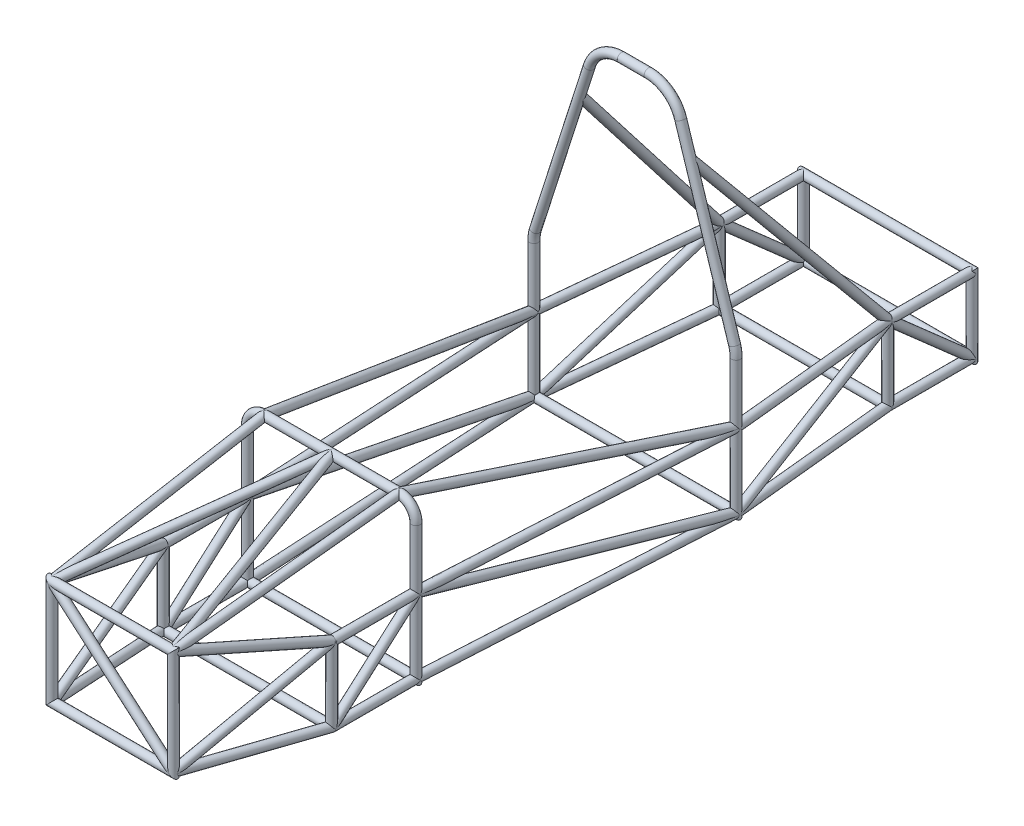
SolidWorks part; units mm, degrees
ref_plane "Front Plane" through (0, 0, 0) normal (0, 0, 1) x (1, 0, 0)
ref_plane "Top Plane" through (0, 0, 0) normal (0, 1, 0) x (1, 0, 0)
ref_plane "Right Plane" through (0, 0, 0) normal (1, 0, 0) x (0, 0, -1)
sketch "Sketch1" plane through (0, 0, 0) normal (0, 0, 1) x (1, 0, 0)
  line L0 (0, 0) -> (0, 400)
  line L1 (4.7576, 430.4776) -> (164.7576, 930.4776)
  line L2 (260, 1000) -> (340, 1000)
  line L3 (435.2424, 930.4776) -> (595.2424, 430.4776)
  line L4 (600, 400) -> (600, 0)
  line L5 (600, 0) -> (0, 0)
  line L6 (300, -975.9464) -> (300, 49024.0536) construction
  arc A0 (595.2424, 430.4776) -> (600, 400) centre (500, 400) cw
  arc A1 (0, 400) -> (4.7576, 430.4776) centre (100, 400) cw
  arc A2 (340, 1000) -> (435.2424, 930.4776) centre (340, 900) cw
  arc A3 (164.7576, 930.4776) -> (260, 1000) centre (260, 900) cw
  dimension "D2" = 100
  dimension "D3" = 100
  dimension "D1" = 600
  dimension "D4" = 300
  dimension "D5" = 400
  dimension "D6" = 80
  dimension "D7" = 1000
sketch "Sketch3" plane through (0, 0, 0) normal (0, 1, 0) x (1, 0, 0)
  line L0 (300, -1107.0637) -> (300, 51069.4933) construction
  dimension "D1" = 300
sketch3d "3DSketch26"
  line L0 (0, 0, 0) -> (50, 0, -500)
  line L2 (550, 0, -500) -> (600, 0, 0)
  line L3 (550, 0, -500) -> (50, 0, -500)
  line L4 (600, 0, 0) -> (0, 0, 0) construction
  dimension "D1" = 500
  dimension "D2" = 500
sketch3d "3DSketch30"
  line L0 (50, 0, -500) -> (50, 220, -500)
  line L2 (550, 220, -500) -> (550, 0, -500)
  dimension "D1" = 220
sketch3d "3DSketch33"
  line L0 (50, 0, -500) -> (50, 0, -750)
  line L1 (50, 0, -750) -> (550, 0, -750)
  line L2 (550, 0, -750) -> (550, 0, -500)
  line L3 (550, 0, -500) -> (50, 0, -500) construction
  dimension "D1" = 250
sketch3d "3DSketch34"
  line L0 (50, 0, -750) -> (50, 220, -750)
  line L1 (50, 220, -750) -> (550, 220, -750)
  line L2 (550, 220, -750) -> (550, 0, -750)
  dimension "D1" = 220
sketch3d "3DSketch35"
  line L0 (50, 220, -500) -> (50, 220, -750)
  line L1 (50, 220, -500) -> (50, 0, -750)
  line L2 (550, 220, -500) -> (550, 220, -750)
  line L3 (550, 220, -500) -> (550, 0, -750)
sketch3d "3DSketch36"
  line L0 (600, 0, 0) -> (550, 220, -500)
  line L1 (0, 0, 0) -> (50, 220, -500)
ref_plane "Plane1" through (0, 0, 900) normal (0, 0, 1) x (1, 0, 0)
sketch "Sketch5" plane through (0, 0, 900) normal (0, 0, 1) x (1, 0, 0)
  line L0 (50, 0) -> (550, 0)
  line L1 (600, 0) -> (0, 0) construction
  line L2 (550, 0) -> (550, 400)
  line L3 (500, 450) -> (100, 450)
  line L4 (50, 400) -> (50, 0)
  arc A0 (550, 400) -> (500, 450) centre (500, 400) ccw
  arc A1 (100, 450) -> (50, 400) centre (100, 400) ccw
  dimension "D1" = 50
  dimension "D2" = 450
  dimension "D3" = 500
  dimension "D4" = 50
sketch3d "3DSketch42"
  line L0 (0, 0, 0) -> (50, 0, 900)
  line L1 (600, 0, 0) -> (550, 0, 900)
sketch3d "3DSketch43"
  line L0 (600, 220, 0) -> (550, 220, 900)
  line L1 (600, 400, 0) -> (600, 0, 0) construction
  line L2 (550, 0, 900) -> (550, 400, 900) construction
  line L3 (550, 220, 900) -> (600, 0, 0)
  line L4 (0, 220, 0) -> (50, 220, 900)
  line L5 (0, 0, 0) -> (0, 400, 0) construction
  line L6 (50, 400, 900) -> (50, 0, 900) construction
  line L7 (50, 220, 900) -> (0, 0, 0)
  dimension "D1" = 220
  dimension "D2" = 220
  dimension "D3" = 220
  dimension "D4" = 220
sketch3d "3DSketch44"
  line L0 (600, 220, 0) -> (500, 450, 900)
  line L1 (0, 220, 0) -> (100, 450, 900)
sketch3d "3DSketch45"
  line L0 (600, 220, 0) -> (550, 220, -500)
  line L1 (0, 220, 0) -> (50, 220, -500)
sketch3d "3DSketch46"
  line L0 (50, 0, 900) -> (50, 0, 1150)
  line L1 (50, 0, 1150) -> (550, 0, 1150)
  line L2 (550, 0, 1150) -> (550, 0, 900)
  dimension "D1" = 250
sketch3d "3DSketch48"
  line L0 (50, 0, 1150) -> (50, 220, 1150)
  line L1 (50, 220, 1150) -> (50, 220, 900)
  line L2 (50, 400, 900) -> (50, 0, 900) construction
  line L3 (50, 0, 1150) -> (50, 220, 900)
  line L4 (550, 0, 1150) -> (550, 220, 1150)
  line L5 (550, 220, 1150) -> (550, 220, 900)
  line L6 (550, 0, 900) -> (550, 400, 900) construction
  line L7 (550, 220, 900) -> (550, 0, 1150)
  dimension "D1" = 220
ref_plane "Plane2" through (0, 0, 1550) normal (0, 0, 1) x (1, 0, 0)
sketch "Sketch6" plane through (0, 0, 1550) normal (0, 0, 1) x (1, 0, 0)
  line L0 (120, 49) -> (480, 49)
  line L1 (480, 49) -> (480, 359)
  line L2 (480, 359) -> (120, 359)
  line L3 (120, 359) -> (120, 49)
  line L4 (0, 0) -> (0, 400) construction
  line L5 (600, 0) -> (0, 0) construction
  dimension "D1" = 360
  dimension "D2" = 310
  dimension "D3" = 120
  dimension "D4" = 49
sketch3d "3DSketch49"
  line L0 (50, 0, 1150) -> (120, 49, 1550)
  line L1 (120, 49, 1550) -> (50, 220, 1150)
  line L2 (50, 220, 1150) -> (120, 359, 1550)
  line L3 (480, 359, 1550) -> (500, 450, 900)
  line L5 (120, 359, 1550) -> (100, 450, 900)
  line L6 (480, 359, 1550) -> (550, 220, 1150)
  line L7 (550, 220, 1150) -> (480, 49, 1550)
  line L8 (480, 49, 1550) -> (480, 359, 1550) construction
  line L9 (120, 49, 1550) -> (480, 49, 1550) construction
  line L10 (480, 49, 1550) -> (550, 0, 1150)
  line L11 (480, 359, 1550) -> (300, 450, 900)
  line L12 (120, 359, 1550) -> (480, 49, 1550)
  line L14 (500, 450, 900) -> (100, 450, 900) construction
  line L15 (300, 450, 900) -> (120, 359, 1550)
sketch "Sketch7" plane through (0, 0, 0) normal (1, 0, 0) x (0, 0, -1)
  line L1 (-517.6033, 105.9189) -> (-104.7916, 369.9008) construction
  line L2 (-104.7916, 369.9008) -> (-104.7916, 649.9008) construction
  line L5 (-900, 450) -> (0, 1009.3878) construction
  line L6 (0, 1000) -> (0, 930.4776) construction
  line L7 (0, -200975.9464) -> (0, 249024.0536) construction
  line L8 (0, 1009.3878) -> (500, 220) construction
  circle A0 centre (-517.6033, 105.9189) radius 100 construction
  arc A1 (-1413.2761, -81.1513) -> (-1357.5003, 468.959) centre (-517.6033, 105.9189) cw construction
  circle A2 centre (-104.7916, 369.9008) radius 100 construction
  circle A3 centre (-104.7916, 649.9008) radius 150 construction
  dimension "D1" = 200
  dimension "D2" = 915
  dimension "D4" = 490
  dimension "D3" = 250
  dimension "D5" = 280
sketch3d "3DSketch51"
  line L0 (50, 220, -500) -> (135.8048, 840, 0)
  line L1 (4.7576, 430.4776, 0) -> (164.7576, 930.4776, 0) construction
  line L2 (550, 220, -500) -> (464.1952, 840, 0)
  line L3 (435.2424, 930.4776, 0) -> (595.2424, 430.4776, 0) construction
  line L4 (260, 1000, 0) -> (340, 1000, 0) construction
  dimension "D1" = 160
sketch3d "3DSketch52"
  line L0 (0, 649.9008, 104.7916) -> (300, 649.9008, 104.7916) construction
  circle A0 centre (300, 649.9008, 104.7916) radius 150 construction
  point P4 (300, 649.9008, 254.7916)
  dimension "D1" = 300
ref_plane "Plane3" through (600, 400, 0) normal (0, -1, 0) x (1, 0, 0)
ref_plane "Plane4" through (595.2424, 430.4776, 0) normal (0.3048, -0.9524, 0) x (0.9524, 0.3048, 0)
ref_plane "Plane5" through (435.2424, 930.4776, 0) normal (0.3048, -0.9524, 0) x (0.9524, 0.3048, 0)
ref_plane "Plane6" through (600, 400, 0) normal (0, -1, 0) x (1, 0, 0)
ref_plane "Plane7" through (600, 0, 0) normal (-0.0555, 0, 0.9985) x (0.9985, 0, 0.0555)
ref_plane "Plane8" through (600, 220, 0) normal (-0.107, 0.2462, 0.9633) x (0.9942, 0.0134, 0.107)
ref_plane "Plane9" through (600, 220, 0) normal (-0.107, 0.2462, 0.9633) x (0.9942, 0.0134, 0.107)
ref_plane "Plane11" through (600, 0, 0) normal (-0.0555, 0, 0.9985) x (0.9985, 0, 0.0555)
ref_plane "Plane12" through (600, 400, 0) normal (0, -1, 0) x (1, 0, 0)
ref_plane "Plane13" through (120, 359, 1550) normal (0.7578, -0.6525, 0) x (0.4258, 0.4945, -0.7578)
ref_plane "Plane14" through (600, 400, 0) normal (0, -1, 0) x (1, 0, 0)
other "Pipe MAIN HOOP(1)"
ref_plane "Plane15" through (600, 400, 0) normal (0, -1, 0) x (1, 0, 0)
sketch "Sketch13" plane through (600, 400, 0) normal (0, -1, 0) x (1, 0, 0)
  circle A0 centre (0, 0) radius 12.7
  circle A1 centre (0, 0) radius 10.3
  point P4 (0, 0)
  dimension "D1" = 25.4
  dimension "D2" = 2.4
other "Pipe MAIN HOOP(2)"
ref_plane "Plane16" through (550, 0, 900) normal (0, 1, 0) x (-1, 0, 0)
sketch "Sketch14" plane through (550, 0, 900) normal (0, 1, 0) x (-1, 0, 0)
  circle A0 centre (0, 0) radius 12.7
  circle A1 centre (0, 0) radius 10.3
  point P4 (0, 0)
  dimension "D1" = 25.4
  dimension "D2" = 2.4
other "Pipe SECONDARY PROFILE(1)"
ref_plane "Plane17" through (480, 49, 1550) normal (0, 1, 0) x (-1, 0, 0)
sketch "Sketch16" plane through (480, 49, 1550) normal (0, 1, 0) x (-1, 0, 0)
  circle A0 centre (0, 0) radius 12.7
  circle A1 centre (0, 0) radius 11.05
  point P4 (0, 0)
  dimension "D1" = 25.4
  dimension "D2" = 1.65
other "Pipe SECONDARY PROFILE(2)"
ref_plane "Plane18" through (600, 220, 0) normal (-0.0555, 0, 0.9985) x (0.9985, 0, 0.0555)
sketch "Sketch17" plane through (600, 220, 0) normal (-0.0555, 0, 0.9985) x (0.9985, 0, 0.0555)
  circle A0 centre (0, 0) radius 12.7
  circle A1 centre (0, 0) radius 11.05
  point P4 (0, 0)
  dimension "D1" = 25.4
  dimension "D2" = 1.65
other "Pipe SECONDARY PROFILE(3)"
ref_plane "Plane19" through (550, 220, 900) normal (0.0539, -0.2371, -0.97) x (0.9032, 0.4257, -0.0539)
sketch "Sketch18" plane through (550, 220, 900) normal (0.0539, -0.2371, -0.97) x (0.9032, 0.4257, -0.0539)
  circle A0 centre (0, 0) radius 12.7
  circle A1 centre (0, 0) radius 11.05
  point P4 (0, 0)
  dimension "D1" = 25.4
  dimension "D2" = 1.65
other "Pipe SECONDARY PROFILE(4)"
ref_plane "Plane20" through (0, 0, 0) normal (0.0555, 0, 0.9985) x (0.9985, 0, -0.0555)
sketch "Sketch19" plane through (0, 0, 0) normal (0.0555, 0, 0.9985) x (0.9985, 0, -0.0555)
  circle A0 centre (0, 0) radius 12.7
  circle A1 centre (0, 0) radius 11.05
  point P4 (0, 0)
  dimension "D1" = 25.4
  dimension "D2" = 1.65
other "Pipe SECONDARY PROFILE(5)"
ref_plane "Plane21" through (50, 220, 900) normal (-0.0539, -0.2371, -0.97) x (0.9032, -0.4257, 0.0539)
sketch "Sketch110" plane through (50, 220, 900) normal (-0.0539, -0.2371, -0.97) x (0.9032, -0.4257, 0.0539)
  circle A0 centre (0, 0) radius 12.7
  circle A1 centre (0, 0) radius 11.05
  point P4 (0, 0)
  dimension "D1" = 25.4
  dimension "D2" = 1.65
other "Pipe TERTIARY PROFILE(1)"
ref_plane "Plane22" through (480, 359, 1550) normal (-0.2645, 0.1337, -0.9551) x (-0.5571, 0.7872, 0.2645)
sketch "Sketch112" plane through (480, 359, 1550) normal (-0.2645, 0.1337, -0.9551) x (-0.5571, 0.7872, 0.2645)
  circle A0 centre (0, 0) radius 12.7
  circle A1 centre (0, 0) radius 11.5
  point P4 (0, 0)
  dimension "D1" = 25.4
  dimension "D2" = 1.2
other "Pipe SECONDARY PROFILE(6)"
ref_plane "Plane23" through (480, 359, 1550) normal (0.0305, 0.1386, -0.9899) x (0.9083, -0.4172, -0.0305)
sketch "Sketch114" plane through (480, 359, 1550) normal (0.0305, 0.1386, -0.9899) x (0.9083, -0.4172, -0.0305)
  circle A0 centre (0, 0) radius 12.7
  circle A1 centre (0, 0) radius 11.05
  point P4 (0, 0)
  dimension "D1" = 25.4
  dimension "D2" = 1.65
other "Pipe SECONDARY PROFILE(7)"
ref_plane "Plane24" through (120, 359, 1550) normal (-0.0305, 0.1386, -0.9899) x (0.9083, 0.4172, 0.0305)
sketch "Sketch115" plane through (120, 359, 1550) normal (-0.0305, 0.1386, -0.9899) x (0.9083, 0.4172, 0.0305)
  circle A0 centre (0, 0) radius 12.7
  circle A1 centre (0, 0) radius 11.05
  point P4 (0, 0)
  dimension "D1" = 25.4
  dimension "D2" = 1.65
other "Pipe SECONDARY PROFILE(8)"
ref_plane "Plane25" through (480, 49, 1550) normal (0.1711, -0.1198, -0.9779) x (-0.3275, 0.9292, -0.1711)
sketch "Sketch116" plane through (480, 49, 1550) normal (0.1711, -0.1198, -0.9779) x (-0.3275, 0.9292, -0.1711)
  circle A0 centre (0, 0) radius 12.7
  circle A1 centre (0, 0) radius 11.05
  point P4 (0, 0)
  dimension "D1" = 25.4
  dimension "D2" = 1.65
other "Pipe SECONDARY PROFILE(10)"
ref_plane "Plane26" through (50, 0, 1150) normal (0.1711, 0.1198, 0.9779) x (0.9852, -0.0104, -0.1711)
sketch "Sketch117" plane through (50, 0, 1150) normal (0.1711, 0.1198, 0.9779) x (0.9852, -0.0104, -0.1711)
  circle A0 centre (0, 0) radius 12.7
  circle A1 centre (0, 0) radius 11.05
  point P4 (0, 0)
  dimension "D1" = 25.4
  dimension "D2" = 1.65
other "Pipe SECONDARY PROFILE(11)"
ref_plane "Plane27" through (120, 49, 1550) normal (-0.1589, 0.3881, -0.9078) x (0.7262, 0.6689, 0.1589)
sketch "Sketch118" plane through (120, 49, 1550) normal (-0.1589, 0.3881, -0.9078) x (0.7262, 0.6689, 0.1589)
  circle A0 centre (0, 0) radius 12.7
  circle A1 centre (0, 0) radius 11.05
  point P4 (0, 0)
  dimension "D1" = 25.4
  dimension "D2" = 1.65
other "Pipe SECONDARY PROFILE(12)"
ref_plane "Plane28" through (550, 220, 1150) normal (-0.1589, -0.3881, 0.9078) x (0.9868, -0.0323, 0.1589)
sketch "Sketch119" plane through (550, 220, 1150) normal (-0.1589, -0.3881, 0.9078) x (0.9868, -0.0323, 0.1589)
  circle A0 centre (0, 0) radius 12.7
  circle A1 centre (0, 0) radius 11.05
  point P4 (0, 0)
  dimension "D1" = 25.4
  dimension "D2" = 1.65
other "Pipe TERTIARY PROFILE(3)"
ref_plane "Plane29" through (120, 359, 1550) normal (0.7578, -0.6525, 0) x (0.4258, 0.4945, -0.7578)
sketch "Sketch121" plane through (120, 359, 1550) normal (0.7578, -0.6525, 0) x (0.4258, 0.4945, -0.7578)
  circle A0 centre (0, 0) radius 12.7
  circle A1 centre (0, 0) radius 11.5
  point P4 (0, 0)
  dimension "D1" = 25.4
  dimension "D2" = 1.2
other "Pipe SECONDARY PROFILE(14)"
ref_plane "Plane31" through (50, 0, 1150) normal (1, 0, 0) x (0, 0, -1)
sketch "Sketch124" plane through (50, 0, 1150) normal (1, 0, 0) x (0, 0, -1)
  circle A0 centre (0, 0) radius 12.7
  circle A1 centre (0, 0) radius 11.05
  point P4 (0, 0)
  dimension "D1" = 25.4
  dimension "D2" = 1.65
other "Pipe TERTIARY PROFILE(4)"
ref_plane "Plane32" through (550, 220, 900) normal (0, -0.6606, 0.7507) x (1, 0, 0)
sketch "Sketch126" plane through (550, 220, 900) normal (0, -0.6606, 0.7507) x (1, 0, 0)
  circle A0 centre (0, 0) radius 12.7
  circle A1 centre (0, 0) radius 11.5
  point P4 (0, 0)
  dimension "D1" = 25.4
  dimension "D2" = 1.2
other "Pipe TERTIARY PROFILE(5)"
ref_plane "Plane33" through (50, 0, 1150) normal (0, 0.6606, -0.7507) x (1, 0, 0)
sketch "Sketch127" plane through (50, 0, 1150) normal (0, 0.6606, -0.7507) x (1, 0, 0)
  circle A0 centre (0, 0) radius 12.7
  circle A1 centre (0, 0) radius 11.5
  point P4 (0, 0)
  dimension "D1" = 25.4
  dimension "D2" = 1.2
other "Pipe SECONDARY PROFILE(15)"
ref_plane "Plane34" through (50, 0, 1150) normal (0, 1, 0) x (1, 0, 0)
sketch "Sketch129" plane through (50, 0, 1150) normal (0, 1, 0) x (1, 0, 0)
  circle A0 centre (0, 0) radius 12.7
  circle A1 centre (0, 0) radius 11.05
  point P4 (0, 0)
  dimension "D1" = 25.4
  dimension "D2" = 1.65
other "Pipe SECONDARY PROFILE(16)"
ref_plane "Plane35" through (550, 0, 1150) normal (0, 1, 0) x (1, 0, 0)
sketch "Sketch130" plane through (550, 0, 1150) normal (0, 1, 0) x (1, 0, 0)
  circle A0 centre (0, 0) radius 12.7
  circle A1 centre (0, 0) radius 11.05
  point P4 (0, 0)
  dimension "D1" = 25.4
  dimension "D2" = 1.65
other "Pipe SECONDARY PROFILE(20)"
ref_plane "Plane40" through (50, 220, -750) normal (1, 0, 0) x (0, 0, -1)
sketch "Sketch135" plane through (50, 220, -750) normal (1, 0, 0) x (0, 0, -1)
  circle A0 centre (0, 0) radius 12.7
  circle A1 centre (0, 0) radius 11.05
  point P4 (0, 0)
  dimension "D1" = 25.4
  dimension "D2" = 1.65
other "Pipe SECONDARY PROFILE(21)"
ref_plane "Plane41" through (550, 0, -500) normal (0.0995, 0, 0.995) x (0.995, 0, -0.0995)
sketch "Sketch136" plane through (550, 0, -500) normal (0.0995, 0, 0.995) x (0.995, 0, -0.0995)
  circle A0 centre (0, 0) radius 12.7
  circle A1 centre (0, 0) radius 11.05
  point P4 (0, 0)
  dimension "D1" = 25.4
  dimension "D2" = 1.65
other "Pipe SECONDARY PROFILE(22)"
ref_plane "Plane42" through (0, 0, 0) normal (0.0995, 0, -0.995) x (-0.995, 0, -0.0995)
sketch "Sketch137" plane through (0, 0, 0) normal (0.0995, 0, -0.995) x (-0.995, 0, -0.0995)
  circle A0 centre (0, 0) radius 12.7
  circle A1 centre (0, 0) radius 11.05
  point P4 (0, 0)
  dimension "D1" = 25.4
  dimension "D2" = 1.65
other "Pipe SECONDARY PROFILE(23)"
ref_plane "Plane43" through (600, 220, 0) normal (-0.0995, 0, -0.995) x (-0.995, 0, 0.0995)
sketch "Sketch138" plane through (600, 220, 0) normal (-0.0995, 0, -0.995) x (-0.995, 0, 0.0995)
  circle A0 centre (0, 0) radius 12.7
  circle A1 centre (0, 0) radius 11.05
  point P4 (0, 0)
  dimension "D1" = 25.4
  dimension "D2" = 1.65
other "Pipe SECONDARY PROFILE(24)"
ref_plane "Plane44" through (0, 220, 0) normal (0.0995, 0, -0.995) x (-0.995, 0, -0.0995)
sketch "Sketch139" plane through (0, 220, 0) normal (0.0995, 0, -0.995) x (-0.995, 0, -0.0995)
  circle A0 centre (0, 0) radius 12.7
  circle A1 centre (0, 0) radius 11.05
  point P4 (0, 0)
  dimension "D1" = 25.4
  dimension "D2" = 1.65
other "Pipe SECONDARY PROFILE(25)"
ref_plane "Plane45" through (50, 0, -500) normal (0, 1, 0) x (1, 0, 0)
sketch "Sketch140" plane through (50, 0, -500) normal (0, 1, 0) x (1, 0, 0)
  circle A0 centre (0, 0) radius 12.7
  circle A1 centre (0, 0) radius 11.05
  point P4 (0, 0)
  dimension "D1" = 25.4
  dimension "D2" = 1.65
other "Pipe SECONDARY PROFILE(26)"
ref_plane "Plane46" through (550, 220, -500) normal (0, -1, 0) x (1, 0, 0)
sketch "Sketch141" plane through (550, 220, -500) normal (0, -1, 0) x (1, 0, 0)
  circle A0 centre (0, 0) radius 12.7
  circle A1 centre (0, 0) radius 11.05
  point P4 (0, 0)
  dimension "D1" = 25.4
  dimension "D2" = 1.65
other "Pipe SECONDARY PROFILE(27)"
ref_plane "Plane47" through (550, 220, -500) normal (-0.1071, 0.7739, 0.6241) x (0.9929, 0.051, 0.1071)
sketch "Sketch142" plane through (550, 220, -500) normal (-0.1071, 0.7739, 0.6241) x (0.9929, 0.051, 0.1071)
  circle A0 centre (0, 0) radius 12.7
  circle A1 centre (0, 0) radius 11.05
  point P4 (0, 0)
  dimension "D1" = 25.4
  dimension "D2" = 1.65
other "Pipe SECONDARY PROFILE(28)"
ref_plane "Plane48" through (50, 220, -500) normal (0.1071, 0.7739, 0.6241) x (0.9929, -0.051, -0.1071)
sketch "Sketch143" plane through (50, 220, -500) normal (0.1071, 0.7739, 0.6241) x (0.9929, -0.051, -0.1071)
  circle A0 centre (0, 0) radius 12.7
  circle A1 centre (0, 0) radius 11.05
  point P4 (0, 0)
  dimension "D1" = 25.4
  dimension "D2" = 1.65
other "Pipe SECONDARY PROFILE(29)"
ref_plane "Plane49" through (550, 0, -500) normal (-1, 0, 0) x (0, 0, 1)
sketch "Sketch144" plane through (550, 0, -500) normal (-1, 0, 0) x (0, 0, 1)
  circle A0 centre (0, 0) radius 12.7
  circle A1 centre (0, 0) radius 11.05
  point P4 (0, 0)
  dimension "D1" = 25.4
  dimension "D2" = 1.65
other "Pipe SECONDARY PROFILE(30)"
ref_plane "Plane50" through (550, 220, -500) normal (0, -0.6606, -0.7507) x (1, 0, 0)
sketch "Sketch145" plane through (550, 220, -500) normal (0, -0.6606, -0.7507) x (1, 0, 0)
  circle A0 centre (0, 0) radius 12.7
  circle A1 centre (0, 0) radius 11.05
  point P4 (0, 0)
  dimension "D1" = 25.4
  dimension "D2" = 1.65
other "Pipe SECONDARY PROFILE(31)"
ref_plane "Plane51" through (600, 0, 0) normal (-0.0912, 0.4011, -0.9115) x (0.9061, 0.4131, 0.0912)
sketch "Sketch146" plane through (600, 0, 0) normal (-0.0912, 0.4011, -0.9115) x (0.9061, 0.4131, 0.0912)
  circle A0 centre (0, 0) radius 12.7
  circle A1 centre (0, 0) radius 11.05
  point P4 (0, 0)
  dimension "D1" = 25.4
  dimension "D2" = 1.65
other "Pipe SECONDARY PROFILE(32)"
ref_plane "Plane52" through (50, 220, -500) normal (0, -0.6606, -0.7507) x (1, 0, 0)
sketch "Sketch147" plane through (50, 220, -500) normal (0, -0.6606, -0.7507) x (1, 0, 0)
  circle A0 centre (0, 0) radius 12.7
  circle A1 centre (0, 0) radius 11.05
  point P4 (0, 0)
  dimension "D1" = 25.4
  dimension "D2" = 1.65
other "Pipe SECONDARY PROFILE(33)"
ref_plane "Plane53" through (0, 0, 0) normal (0.0912, 0.4011, -0.9115) x (0.9061, -0.4131, -0.0912)
sketch "Sketch148" plane through (0, 0, 0) normal (0.0912, 0.4011, -0.9115) x (0.9061, -0.4131, -0.0912)
  circle A0 centre (0, 0) radius 12.7
  circle A1 centre (0, 0) radius 11.05
  point P4 (0, 0)
  dimension "D1" = 25.4
  dimension "D2" = 1.65
